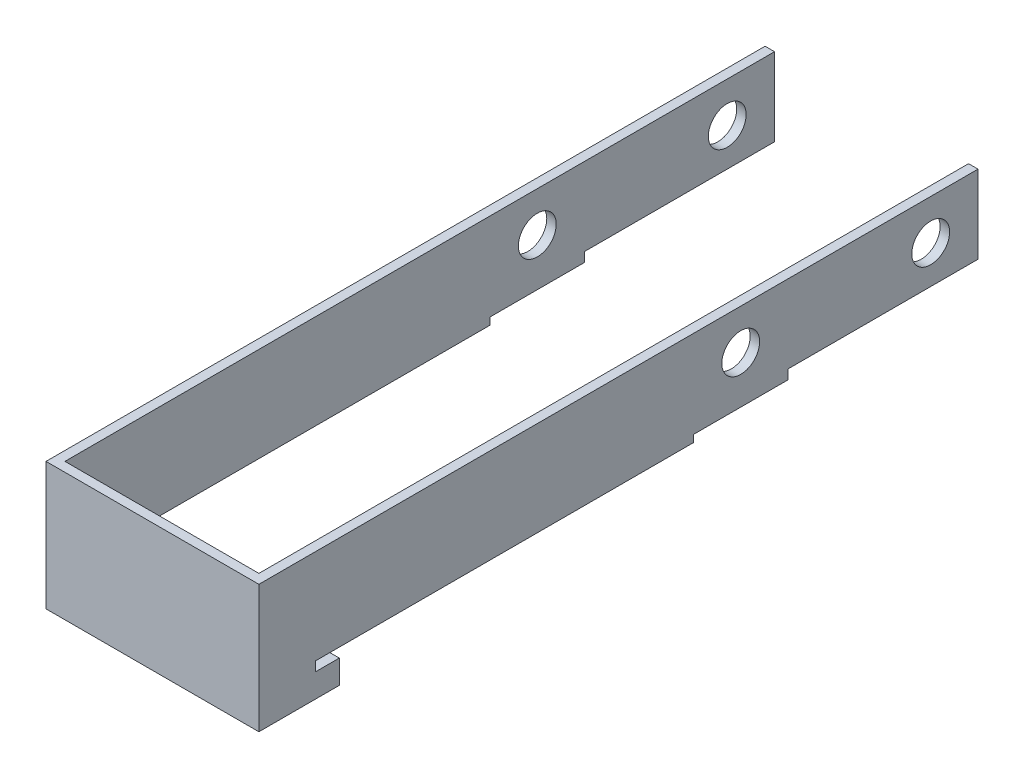
SolidWorks part; units mm, degrees
material "AISI 304"
ref_plane "Front Plane" through (0, 0, 0) normal (1, 0, 0) x (0, 1, 0)
ref_plane "Top Plane" through (0, 0, 0) normal (0, 0, 1) x (0, 1, 0)
ref_plane "Right Plane" through (0, 0, 0) normal (0, 1, 0) x (-1, 0, 0)
sketch "Sketch1" plane through (0, 0, 0) normal (1, 0, 0) x (0, 1, 0)
  line L0 (8.5, -10) -> (8.5, 140)
  line L1 (8.5, 140) -> (-18.5, 140)
  line L2 (-18.5, 140) -> (-18.5, 125)
  line L3 (-18.5, 125) -> (-13.5, 125)
  line L4 (-13.5, 125) -> (-13.5, 130)
  line L5 (-13.5, 130) -> (-11.5, 130)
  line L6 (-11.5, 130) -> (-11.5, 50.1528)
  line L7 (-11.5, 50.1528) -> (-10, 50.1528)
  line L8 (-10, 50.1528) -> (-10, 30.1528)
  line L9 (-10, 30.1528) -> (-8, 30.1528)
  line L10 (-8, 30.1528) -> (-8, -10)
  line L11 (-8, -10) -> (8.5, -10)
  line L12 (0, 0) -> (0, 40.1528) construction
  circle A0 centre (0, 0) radius 4
  circle A1 centre (0, 40.1528) radius 4
  point P16 (0, 0)
  point P17 (-10, 40.1528)
  point P19 (-10.718, 40)
  point P21 (-10.718, 40)
  point P22 (0, 41.411)
  point P23 (0, 39.0556)
  point P24 (0, 40.1208)
  point P25 (0, 36.6715)
  point P26 (0, 40.1528)
  dimension "D2" = 8
  dimension "D3" = 8
  dimension "D4" = 8.5
  dimension "D5" = 8
  dimension "D6" = 10
  dimension "D7" = 10
  dimension "D8" = 10
  dimension "D9" = 20
  dimension "D10" = 5
  dimension "D11" = 140
  dimension "D12" = 2
  dimension "D13" = 5
  dimension "D14" = 10
extrude "Boss-Extrude1" add sketch "Sketch1" against normal blind 2
ref_plane "Plane1" through (-22.5, 0, 0) normal (-1, 0, 0) x (0, 1, 0)
mirror "Mirror2" about plane through (-22.5, 0, 0) normal (-1, 0, 0) of bodies 101
sketch "Sketch2" plane through (0, 0, 140) normal (0, 0, 1) x (1, 0, 0)
  line L1 (-45, 8.5) -> (0, 8.5)
  line L2 (-45, 8.5) -> (-45, -18.5)
  line L3 (-45, -18.5) -> (0, -18.5)
  line L4 (0, 8.5) -> (0, -18.5)
extrude "Boss-Extrude2" add sketch "Sketch2" along normal blind 2
